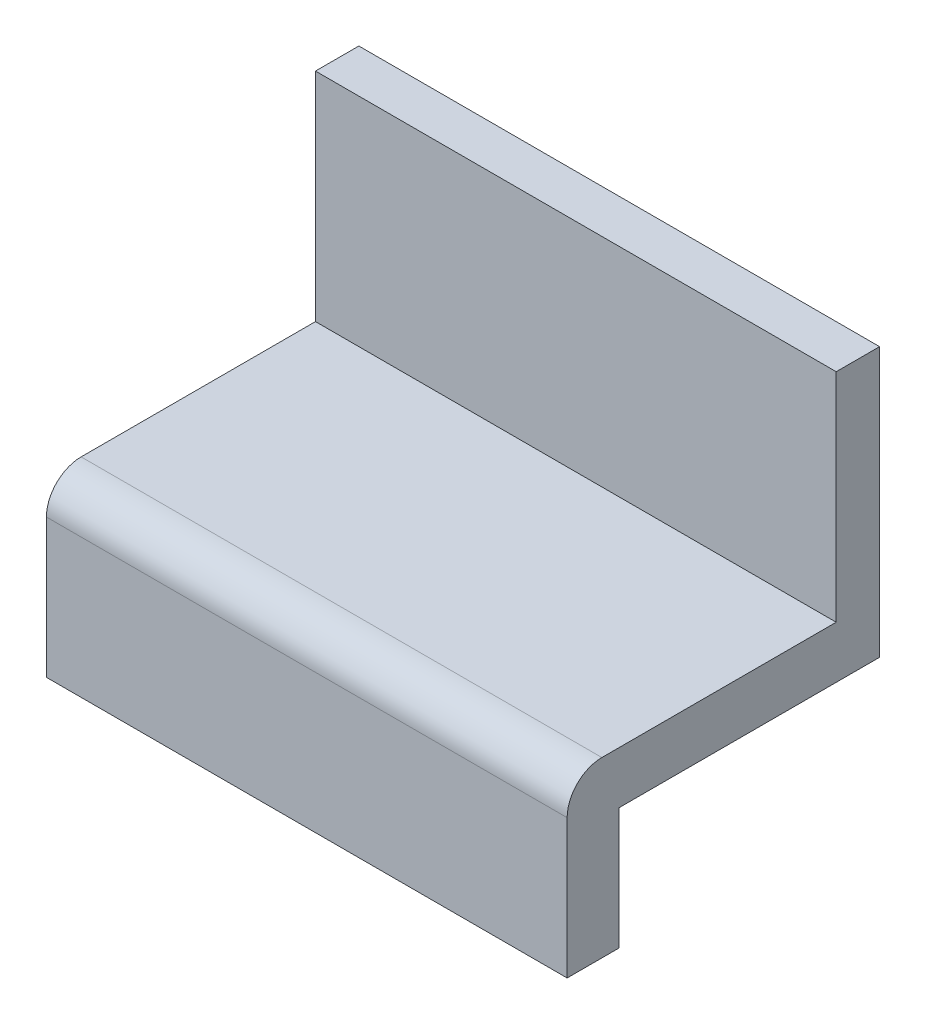
SolidWorks part; units mm, degrees
ref_plane "정면" through (0, 0, 0) normal (0, 0, 1) x (1, 0, 0)
ref_plane "윗면" through (0, 0, 0) normal (0, 1, 0) x (1, 0, 0)
ref_plane "우측면" through (0, 0, 0) normal (1, 0, 0) x (0, 0, -1)
sketch "스케치1" plane through (0, 0, 0) normal (0, 1, 0) x (1, 0, 0)
  line L0 (-24.6337, 0) -> (23.9498, 0) construction
  line L1 (0, 18.2757) -> (0, -20.9974) construction
  line L3 (15, -9) -> (-15, -9)
  line L4 (15, -9) -> (15, 9)
  line L5 (15, 9) -> (-15, 9)
  line L6 (-15, -9) -> (-15, 9)
  line L7 (15, -9) -> (-15, 9) construction
  line L8 (15, 9) -> (-15, -9) construction
  point P5 (0, 0)
  point P10 (-24.6337, 0)
  point P11 (23.9498, 0)
  point P12 (0, 18.2757)
  point P13 (0, -20.9974)
  dimension "D1" = 30
  dimension "D2" = 18
extrude "보스-돌출1" add sketch "스케치1" along normal blind 3
sketch "스케치2" plane through (0, 0, 0) normal (0, -1, 0) x (1, 0, 0)
  line L0 (15, 9) -> (15, -9) construction
  line L1 (-15, 9) -> (15, 9)
  line L2 (-15, 9) -> (-15, 6)
  line L3 (-15, 6) -> (15, 6)
  line L4 (15, 9) -> (15, 6)
  dimension "D1" = 3
extrude "보스-돌출2" add sketch "스케치2" along normal blind 7
fillet "필렛1" radius 2 1 edges at (0, 3, 9)
sketch "스케치5" plane through (0, 3, 0) normal (0, 1, 0) x (1, 0, 0)
  line L0 (-15, 9) -> (-15, -7) construction
  line L1 (-15, 6.5) -> (15, 6.5)
  line L2 (-15, 6.5) -> (-15, 9)
  line L3 (-15, 9) -> (15, 9)
  line L4 (15, 6.5) -> (15, 9)
  line L5 (15, -7) -> (15, 9) construction
  line L7 (15, 9) -> (-15, 9) construction
  dimension "D2" = 2.5
extrude "보스-돌출3" add sketch "스케치5" along normal blind 12.5
